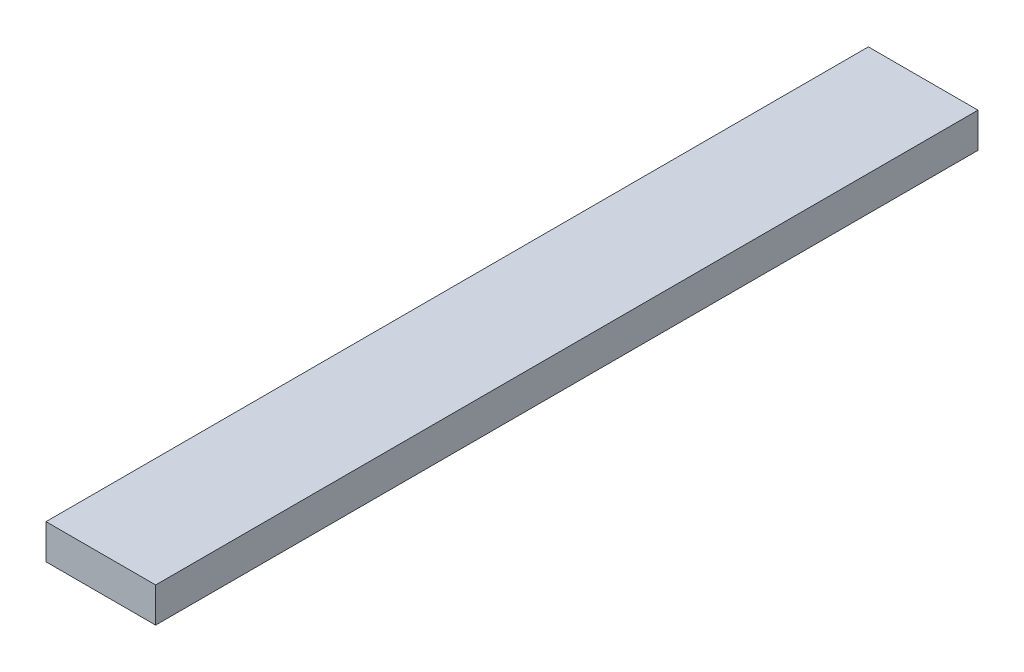
SolidWorks part; units mm, degrees
ref_plane "Front Plane" through (0, 0, 0) normal (0, 0, 1) x (1, 0, 0)
ref_plane "Top Plane" through (0, 0, 0) normal (0, 1, 0) x (1, 0, 0)
ref_plane "Right Plane" through (0, 0, 0) normal (1, 0, 0) x (0, 0, -1)
sketch "Sketch1" plane through (0, 0, 0) normal (0, 1, 0) x (1, 0, 0)
  line L1 (0, 150) -> (20, 150)
  line L2 (0, 150) -> (0, 0)
  line L3 (0, 0) -> (20, 0)
  line L4 (20, 150) -> (20, 0)
  point P9 (0, 0)
  dimension "D1" = 150
  dimension "D2" = 20
extrude "Boss-Extrude1" add sketch "Sketch1" along normal blind 6.35
